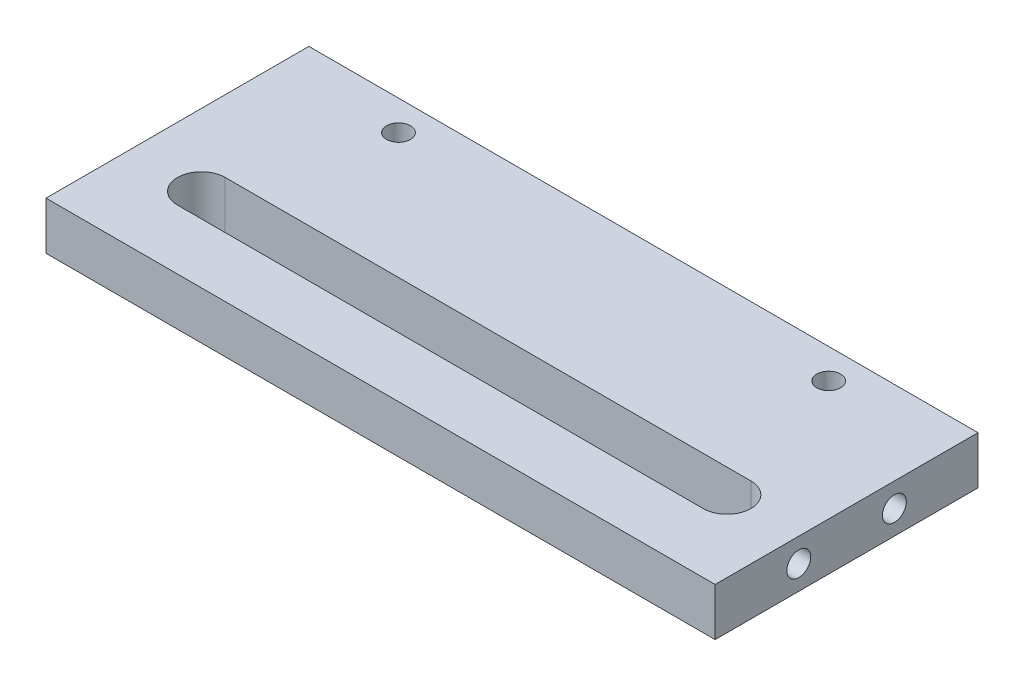
SolidWorks part; units mm, degrees
ref_plane "Alzado" through (0, 0, 0) normal (0, 0, 1) x (1, 0, 0)
ref_plane "Planta" through (0, 0, 0) normal (0, 1, 0) x (1, 0, 0)
ref_plane "Vista lateral" through (0, 0, 0) normal (1, 0, 0) x (0, 0, -1)
sketch "Croquis1" plane through (0, 0, 0) normal (0, 1, 0) x (1, 0, 0)
  line L1 (-125.7057, 56.7568) -> (154.2943, 56.7568)
  line L2 (-125.7057, 56.7568) -> (-125.7057, -53.2432)
  line L3 (-125.7057, -53.2432) -> (154.2943, -53.2432)
  line L4 (154.2943, 56.7568) -> (154.2943, -53.2432)
  dimension "D1" = 280
  dimension "D2" = 110
extrude "Saliente-Extruir1" add sketch "Croquis1" along normal blind 20
sketch "Croquis2" plane through (0, 0, 0) normal (0, 1, 0) x (1, 0, 0)
  line L0 (154.2943, 56.7568) -> (-125.7057, 56.7568) construction
  line L1 (-95.7057, -8.2432) -> (124.2943, -8.2432)
  line L3 (-95.7057, -28.2432) -> (124.2943, -28.2432)
  line L4 (-125.7057, 56.7568) -> (-125.7057, -53.2432) construction
  arc A0 (124.2943, -28.2432) -> (124.2943, -8.2432) centre (124.2943, -18.2432) ccw
  arc A1 (-95.7057, -8.2432) -> (-95.7057, -28.2432) centre (-95.7057, -18.2432) ccw
  dimension "D4" = 30
  dimension "D1" = 65
  dimension "D2" = 20
  dimension "D3" = 220
extrude "Cortar-Extruir2" cut sketch "Croquis2" along normal blind 20
sketch "Croquis4" plane through (0, 0, 0) normal (0, 1, 0) x (1, 0, 0)
  line L0 (-125.7057, 56.7568) -> (-125.7057, -53.2432) construction
  circle A1 centre (104.2943, 44.2568) radius 5
  circle A2 centre (-75.7057, 44.2568) radius 5
  dimension "D1" = 50
  dimension "D5" = 180
extrude "Cortar-Extruir4" cut sketch "Croquis4" along normal blind 20
sketch "Croquis5" plane through (-125.7057, 0, 0) normal (-1, 0, 0) x (0, 0, 1)
  line L0 (53.2432, 20) -> (53.2432, 0) construction
  line L2 (-56.7568, 20) -> (-56.7568, 0) construction
  line L3 (-56.7568, 20) -> (53.2432, 20) construction
  circle A0 centre (18.2432, 10) radius 5
  circle A1 centre (-21.7568, 10) radius 5
  dimension "D3" = 10
  dimension "D6" = 10
  dimension "D1" = 35
  dimension "D2" = 10
  dimension "D4" = 35
  dimension "D5" = 10
extrude "Cortar-Extruir5" cut sketch "Croquis5" against normal blind 18
sketch "Croquis6" plane through (154.2943, 0, 0) normal (1, 0, 0) x (0, 0, -1)
  line L1 (-53.2432, 20) -> (-53.2432, 0) construction
  line L2 (56.7568, 20) -> (56.7568, 0) construction
  line L3 (-53.2432, 0) -> (56.7568, 0) construction
  circle A0 centre (21.7568, 10) radius 5
  circle A1 centre (-18.2432, 10) radius 5
  dimension "D1" = 10
  dimension "D2" = 10
  dimension "D3" = 10
  dimension "D4" = 10
  dimension "D5" = 35
  dimension "D6" = 35
extrude "Cortar-Extruir6" cut sketch "Croquis6" against normal blind 18
